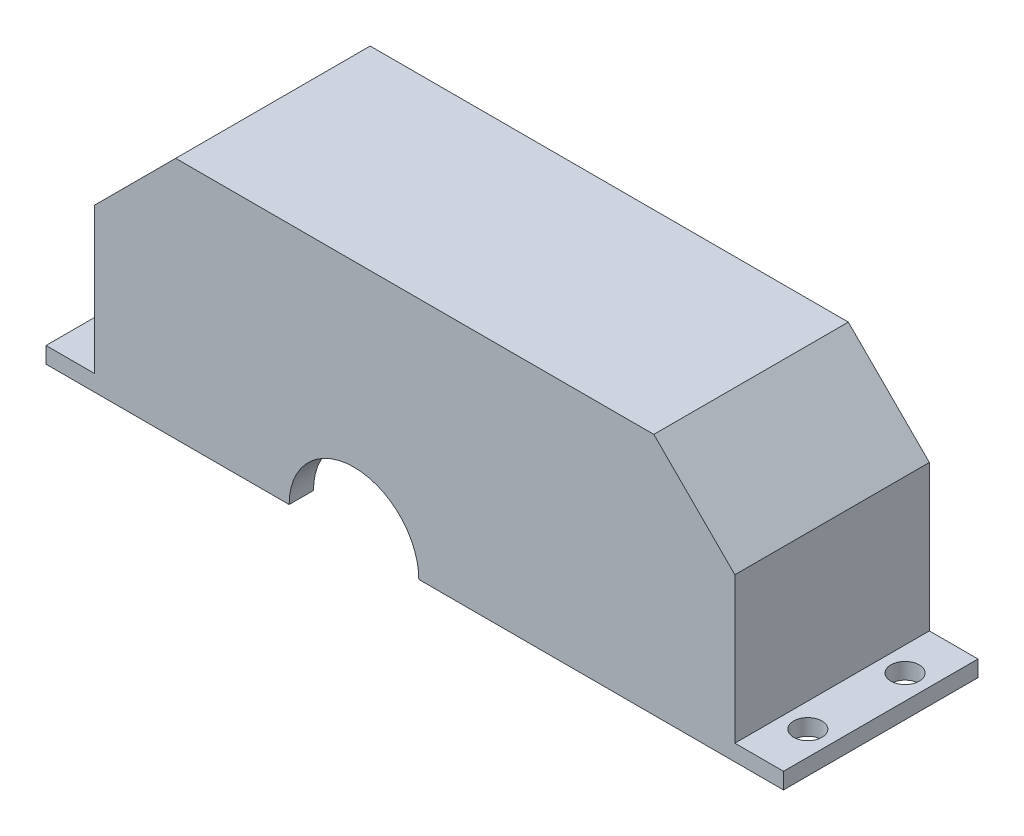
SolidWorks part; units mm, degrees
ref_plane "Alzado" through (0, 0, 0) normal (0, 0, 1) x (1, 0, 0)
ref_plane "Planta" through (0, 0, 0) normal (0, 1, 0) x (1, 0, 0)
ref_plane "Vista lateral" through (0, 0, 0) normal (1, 0, 0) x (0, 0, -1)
sketch "Croquis1" plane through (0, 0, 0) normal (0, 0, 1) x (1, 0, 0)
  line L3 (0, 0) -> (24, 0)
  line L4 (73, 0) -> (79, 0)
  line L8 (0, 30) -> (0, 0)
  line L9 (79, 30) -> (79, 0)
  line L10 (79, 30) -> (0, 30)
  line L11 (73, 0) -> (73, 12)
  line L12 (73, 12) -> (46, 12)
  line L13 (46, 12) -> (46, 0)
  line L14 (40, 0) -> (46, 0)
  arc A3 (40, 0) -> (24, 0) centre (32, 0) ccw
  dimension "D4" = 12
  dimension "D6" = 16
  dimension "D8" = 12
  dimension "D1" = 6
  dimension "D7" = 30
  dimension "D5" = 79
  dimension "D2" = 6
  dimension "D3" = 30
  dimension "D9" = 32
extrude "Saliente-Extruir1" add sketch "Croquis1" along normal blind 5
sketch "Croquis4" plane through (0, 0, 5) normal (0, 0, 1) x (1, 0, 0)
  line L14 (0, 30) -> (0, 0)
  line L21 (0, 30) -> (79, 30)
  line L22 (79, 30) -> (79, 0)
  line L23 (79, 0) -> (76, 0)
  line L24 (76, 0) -> (76, 27)
  line L25 (76, 27) -> (3, 27)
  line L26 (3, 27) -> (3, 0)
  line L27 (3, 0) -> (0, 0)
  dimension "D3" = 3
  dimension "D1" = 3
  dimension "D2" = 3
extrude "Saliente-Extruir4" add sketch "Croquis4" along normal blind 15
sketch "Croquis6" plane through (0, 0, 20) normal (0, 0, 1) x (1, 0, 0)
  line L7 (0, 0) -> (0, 30)
  line L8 (0, 30) -> (79, 30)
  line L9 (79, 30) -> (79, 0)
  line L14 (79, 0) -> (40, 0)
  line L15 (24, 0) -> (0, 0)
  arc A6 (40, 0) -> (24, 0) centre (32, 0) ccw
extrude "Saliente-Extruir6" add sketch "Croquis6" along normal blind 3
sketch "Croquis13" plane through (0, 0, 0) normal (0, 0, -1) x (-1, 0, 0)
  line L0 (-79, 30) -> (-79, 0)
  line L1 (-73, 0) -> (-79, 0) construction
  line L2 (-79, 0) -> (-73, 0)
  line L3 (-73, 0) -> (-73, 12)
  line L5 (-46, 12) -> (-46, 0)
  line L6 (-46, 0) -> (-40, 0)
  line L7 (-79, 30) -> (0, 30)
  line L8 (0, 30) -> (0, 0)
  line L10 (-73, 12) -> (-46, 12)
  line L11 (-40, 0) -> (-38, 0)
  line L13 (0, 0) -> (-26, 0)
  line L15 (-40, 0) -> (-46, 0) construction
  line L16 (-46, 12) -> (-46, 0) construction
  arc A2 (-26, 0) -> (-38, 0) centre (-32, 0) ccw
  arc A3 (-24, 0) -> (-40, 0) centre (-32, 0) ccw construction
  dimension "D2" = 12
extrude "Saliente-Extruir10" add sketch "Croquis13" along normal blind 1
sketch "Croquis8" plane through (79, 0, 0) normal (1, 0, 0) x (0, 0, -1)
  line L1 (-23, 0) -> (1, 0)
  line L2 (-23, 0) -> (-23, 2)
  line L3 (-23, 2) -> (1, 2)
  line L4 (1, 0) -> (1, 2)
  line L5 (-23, 0) -> (-23, 30) construction
  dimension "D1" = 2
extrude "Saliente-Extruir8" add sketch "Croquis8" along normal blind 6
sketch "Croquis18" plane through (0, 0, 0) normal (-1, 0, 0) x (0, 0, 1)
  line L1 (-1, 0) -> (23, 0)
  line L2 (-1, 0) -> (-1, 2)
  line L3 (-1, 2) -> (23, 2)
  line L4 (23, 0) -> (23, 2)
  line L5 (23, 30) -> (23, 0) construction
  dimension "D1" = 2
extrude "Saliente-Extruir14" add sketch "Croquis18" along normal blind 6
sketch "Croquis12" plane through (0, 2, 0) normal (0, 1, 0) x (1, 0, 0)
  line L4 (39.5, 1) -> (39.5, -26) construction
  line L5 (-6, 1) -> (0, 1) construction
  line L6 (-6, -23) -> (0, -23) construction
  line L8 (0, 1) -> (79, 1) construction
  circle A0 centre (-3, -5) radius 1.75
  circle A2 centre (-3, -17) radius 1.75
  circle A3 centre (82, -17) radius 1.75
  circle A5 centre (82, -5) radius 1.75
  dimension "D1" = 3.5
  dimension "D2" = 6
  dimension "D3" = 3.5
  dimension "D4" = 6
extrude "Cortar-Extruir1" cut sketch "Croquis12" against normal through all both and the other way through all
chamfer "Chaflán4" distance 7 angle 45 2 edges at (3, 27, 12.5) (76, 27, 12.5)
chamfer "Chaflán5" distance 10 angle 45 2 edges at (0, 30, 11) (79, 30, 11)
fillet "Redondeo1" radius 3 2 edges at (46, 12, 2) (73, 12, 2)
